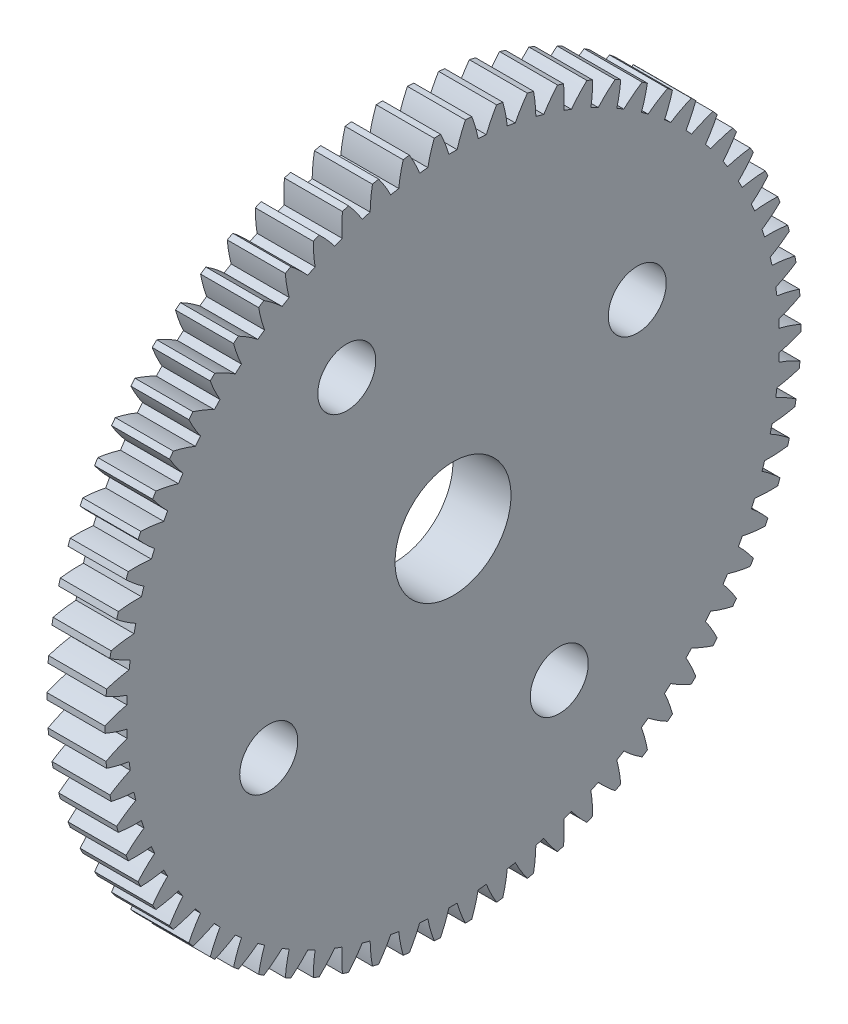
SolidWorks part; units mm, degrees
ref_plane "Plane1" through (0, 0, 0) normal (0, 0, 1) x (1, 0, 0)
ref_plane "Plane2" through (0, 0, 0) normal (0, 1, 0) x (1, 0, 0)
ref_plane "Plane3" through (0, 0, 0) normal (1, 0, 0) x (0, 0, -1)
sketch "HoldingSke" plane through (0, 0, 0) normal (0, 1, 0) x (1, 0, 0)
  line L0 (0, 0) -> (0.684, -1.8794)
  line L1 (-15, 0) -> (100, 0) construction
  line L2 (0, 0) -> (-2.1039, 2.3779)
  line L3 (0, 0) -> (-11.863, 4.5341)
  line L4 (0, 0) -> (2.9537, 8.1152)
  line L5 (0, 0) -> (-7.4956, -2.7956)
  line L6 (0, 0) -> (-2.4869, -1.6779)
  line L7 (-2.1039, 2.3779) -> (-0.3819, 10.1904)
  line L8 (-76.2, 54.61) -> (-75.2, 54.61)
  line L9 (-71.009, 38.7566) -> (-53.1078, 45.2721)
  line L10 (-76.2, 71.12) -> (104.1128, 71.12)
  line L11 (0, 0) -> (-3, 0)
  line L12 (-76.2, 101.6) -> (-76.181, 101.6)
  line L13 (24.9733, 27.94) -> (52.9518, 28.4284)
  line L14 (24.9733, 27.94) -> (24.9743, 27.94)
  line L15 (24.9733, 27.94) -> (100.4006, 29.5858)
  line L16 (-63.627, -0.5) -> (-12.827, -0.5)
  circle A0 centre (0, 0) radius 3
  circle A1 centre (0, 0) radius 7
  circle A2 centre (0, 0) radius 7
  circle A3 centre (0, 0) radius 3
  dimension "MHD" = 14
  dimension "Hub_dia" = 14
  dimension "Bore" = 6
  dimension "MBD" = 6
  dimension "Num_teeth" = 70
  dimension "Pitch" = 2
  dimension "Overall_len" = 8
  dimension "Show_teeth" = 70
  dimension "Thickness" = 3
  dimension "OAL" = 8.0001
  dimension "T_dim" = 1
  dimension "Ap" = 20
  dimension "H" = 19.05
  dimension "Pitch_radius" = 180.3128
  dimension "Width" = 3
  dimension "Backlash" = 0.019
  dimension "Addendum_fac" = 1
  dimension "Dedendum_fac" = 1.25
  dimension "Clearance_fac" = 0.25
  dimension "Dedendum_add" = 0.001
  dimension "Module" = 0.5
sketch "BasProSke" plane through (0, 0, 0) normal (0, 1, 0) x (1, 0, 0)
  line L0 (-10, 0) -> (60, 0) construction
  line L1 (0, 0) -> (0, 18)
  line L2 (0, 0) -> (3, 0)
  line L3 (3, 0) -> (3, 18)
  line L4 (3, 18) -> (0, 18)
  dimension "Thickness" = 3
  dimension "Diameter" = 36
revolve "Base-Revolve" add sketch "BasProSke" angle 360 about L0
sketch "TooCutSke" plane through (0, 0, 0) normal (1, 0, 0) x (0, 0, -1)
  line L1 (0, 0) -> (0, 107) construction
  line L2 (0, 0) -> (-0.4259, 17.4948) construction
  line L3 (0, 0) -> (-1.5699, 34.9574) construction
  line L4 (-0.4259, 17.4948) -> (-0.785, 17.4787) construction
  arc A0 (0.2122, 16.8727) -> (-0.2122, 16.8727) centre (0, 0) ccw
  arc A1 (0.6565, 18.0134) -> (-0.6565, 18.0134) centre (0, 0) ccw
  circle A2 centre (0, 0) radius 17.5 construction
  circle A3 centre (0, 0) radius 16.4446 construction
  arc A4 (-0.2122, 16.8727) -> (-0.6565, 18.0134) centre (-6.9321, 14.9121) ccw
  arc A5 (0.6565, 18.0134) -> (0.2122, 16.8727) centre (6.9321, 14.9121) ccw
  dimension "Root_dia" = 33.748
  dimension "Overcut_dia" = 36.0508
  dimension "Pitch_dia" = 35
  dimension "Base_dia" = 32.8892
  dimension "Flank_rad" = 7
  dimension "Half_ang" = 2.571
  dimension "Half_CT" = 0.3594
extrude "ToothCut" cut sketch "TooCutSke" along normal through all
fillet "Breaks" [suppressed] radius 0.01
fillet "RootFillets" [suppressed] radius 0.126
pattern_circular "TeethCuts" count 70 every 5.143 about axis through (-10, 0, 0) along (1, 0, 0) of "ToothCut", "RootFillets", "Breaks"
sketch "HubNeaOneSke" plane through (0, 0, 0) normal (-1, 0, 0) x (0, 0, 1)
  circle A0 centre (0, 0) radius 7
  dimension "Diameter" = 14
sketch "HubNeaBotSke" plane through (0, 0, 0) normal (-1, 0, 0) x (0, 0, 1)
  circle A0 centre (0, 0) radius 7
  dimension "Diameter" = 14
extrude "HubNearBoth" [suppressed] add sketch "HubNeaBotSke" along normal blind 2.5
ref_plane "FarPln" through (3, 0, 0) normal (1, 0, 0) x (0, 0, -1)
sketch "HubFarSke" plane through (3, 0, 0) normal (1, 0, 0) x (0, 0, -1)
  circle A0 centre (0, 0) radius 7
  dimension "Diameter" = 14
extrude "HubFar" [suppressed] add sketch "HubFarSke" along normal blind 2.5
sketch "BorSke" plane through (0, 0, 0) normal (1, 0, 0) x (0, 0, -1)
  circle A0 centre (0, 0) radius 3
  dimension "Diameter" = 6
extrude "Bore" cut sketch "BorSke" along normal mid plane 16.0001
sketch "KeySke" plane through (0, 0, 0) normal (1, 0, 0) x (0, 0, -1)
  line L0 (-1, 0) -> (-1, 4)
  line L1 (-1, 4) -> (1, 4)
  line L2 (1, 4) -> (1, 0)
  line L3 (0, 0) -> (0, 34) construction
  line L4 (-1, 0) -> (1, 0)
  dimension "Offset" = 4
  dimension "Width" = 2
extrude "Keyway" [suppressed] cut sketch "KeySke" along normal mid plane 16.0001
pattern_circular "Keyway2" [suppressed] count 2 every 90 about axis through (-10, 0, 0) along (1, 0, 0)
sketch "Sketch1" plane through (3, 0, 0) normal (1, 0, 0) x (0, 0, -1)
  circle A0 centre (0, 0) radius 8
  circle A1 centre (0, 8) radius 1.05
  circle A2 centre (8, 0) radius 1.05
  circle A3 centre (0, -8) radius 1.05
  circle A4 centre (-8, 0) radius 1.05
  point P14 (0, 0)
  dimension "D1" = 16
  dimension "D2" = 2.1
  dimension "D3" = 4
extrude "Cut-Extrude1" [suppressed] cut sketch "Sketch1" against normal blind 10 contours A4 | A2 | A3 | A1
sketch "Sketch3" plane through (0, 0, 0) normal (-1, 0, 0) x (0, 0, 1)
  circle A0 centre (0, 0) radius 14.5
  circle A1 centre (0, 0) radius 7.5
  dimension "D1" = 29
  dimension "D2" = 15
extrude "Cut-Extrude3" cut sketch "Sketch3" against normal blind 0.5
sketch "Sketch4" plane through (0.5, 0, 0) normal (-1, 0, 0) x (0, 0, 1)
  circle A0 centre (0, 0) radius 11 construction
  circle A1 centre (5.4948, 9.5293) radius 1.5
  circle A2 centre (9.5293, -5.4948) radius 1.5
  circle A3 centre (-5.4948, -9.5293) radius 1.5
  circle A4 centre (-9.5293, 5.4948) radius 1.5
  point P14 (0, 0)
  dimension "D1" = 22
  dimension "D2" = 3
  dimension "D3" = 4
extrude "Cut-Extrude4" cut sketch "Sketch4" against normal through all
equation "' \"Module@HoldingSke\" = 6.35"
equation "' \"Num_teeth@HoldingSke\" = 12"
equation "' \"Ap@HoldingSke\" =  20"
equation "' \"Ap@HoldingSke\" = 20"
equation "' \"Width@HoldingSke\" = 0.5 * 25.4"
equation "' \"Hub_dia@HoldingSke\"= 1 * 25.4"
equation "' \"Hub_dia@HoldingSke\" = 1 * 25.4"
equation "' \"Overall_len@HoldingSke\" = 1.0 * 25.4"
equation "' \"Bore@HoldingSke\" = 0.75 * 25.4"
equation "' \"T_dim@HoldingSke\" = 0.1 * 25.4"
equation "' \"Width@KeySke\" = 0.25 * 25.4"
equation "' \"Show_teeth@HoldingSke\" = 13"
equation "' \"Backlash@HoldingSke\" = 0.009 * 25.4"
equation "' \"Addendum_fac@HoldingSke\" = 1.0"
equation "' \"Dedendum_fac@HoldingSke\" = 1.25"
equation "' \"Dedendum_add@HoldingSke\" = 0.00005 * 25.4"
equation "' \"Clearance_fac@HoldingSke\" = 0.25"
equation "\"Pitch@HoldingSke\" = 1 / \"Module@HoldingSke\""
equation "\"Overcut_dia@TooCutSke\" = (\"Num_teeth@HoldingSke\" + 2 * \"Addendum_fac@HoldingSke\") / \"Pitch@HoldingSke\" + 0.002 * 25.4"
equation "\"Pitch_dia@TooCutSke\" = \"Num_teeth@HoldingSke\" / \"Pitch@HoldingSke\""
equation "\"Base_dia@TooCutSke\" = \"Num_teeth@HoldingSke\" / \"Pitch@HoldingSke\" * cos((\"Ap@HoldingSke\"  * 3.14159265 / 180))"
equation "\"Root_dia@TooCutSke\" = (\"Num_teeth@HoldingSke\" + 2) / \"Pitch@HoldingSke\" - 2 * (\"Addendum_fac@HoldingSke\" + \"Dedendum_fac@HoldingSke\") / \"Pitch@HoldingSke\" - \"Dedendum_add@HoldingSke\" * 2"
equation "\"Half_ang@TooCutSke\" = 180 / \"Num_teeth@HoldingSke\""
equation "\"Half_CT@TooCutSke\" = \"Num_teeth@HoldingSke\" / \"Pitch@HoldingSke\" * sin((3.14159265 / 2 / \"Num_teeth@HoldingSke\")) / 2 - 7 * \"Backlash@HoldingSke\" / 4"
equation "\"Flank_rad@TooCutSke\" = \"Num_teeth@HoldingSke\" / \"Pitch@HoldingSke\" / 5"
equation "\"Radius@RootFillets\" = \"Clearance_fac@HoldingSke\" / \"Pitch@HoldingSke\" + \"Dedendum_add@HoldingSke\""
equation "\"Break_rad@Breaks\" = 0.02 / \"Pitch@HoldingSke\""
equation "\"Thickness@HoldingSke\" = \"Width@HoldingSke\""
equation "\"OAL@HoldingSke\" = \"Thickness@HoldingSke\""
equation "\"MHD@HoldingSke\" = (\"Num_teeth@HoldingSke\" + 2) / \"Pitch@HoldingSke\" - 2 * (\"Addendum_fac@HoldingSke\" + \"Dedendum_fac@HoldingSke\")  / \"Pitch@HoldingSke\" - \"Dedendum_add@HoldingSke\" * 2"
equation "\"MBD@HoldingSke\" = (\"Num_teeth@HoldingSke\" + 2) / \"Pitch@HoldingSke\" - 2 * (\"Addendum_fac@HoldingSke\" + \"Dedendum_fac@HoldingSke\")  / \"Pitch@HoldingSke\" - \"Dedendum_add@HoldingSke\" * 2 - 0.002 * 25.4"
equation "\"MHD@HoldingSke\" = ((sgn( \"MHD@HoldingSke\" - \"Hub_dia@HoldingSke\" )-1)*( \"MHD@HoldingSke\" - \"Hub_dia@HoldingSke\" ))/-2+ \"Hub_dia@HoldingSke\""
equation "\"MBD@HoldingSke\" = ((sgn( \"MBD@HoldingSke\" - \"Bore@HoldingSke\" )-1)*( \"MBD@HoldingSke\" - \"Bore@HoldingSke\" ))/-2+ \"Bore@HoldingSke\""
equation "\"OAL@HoldingSke\" = ((sgn( \"OAL@HoldingSke\" - \"Overall_len@HoldingSke\" )+1)*( \"OAL@HoldingSke\" - \"Overall_len@HoldingSke\" ))/2 + \"Overall_len@HoldingSke\" + 0.000002 * 25.4"
equation "\"Num_teeth@TeethCuts\" = int( \"Show_teeth@HoldingSke\" ) + 1"
equation "\"Num_teeth@TeethCuts\" = ((sgn( \"Num_teeth@TeethCuts\" - \"Num_teeth@HoldingSke\" )-1)*( \"Num_teeth@TeethCuts\" - \"Num_teeth@HoldingSke\" ))/-2+ \"Num_teeth@HoldingSke\""
equation "\"Num_teeth@TeethCuts\" = ((sgn( \"Num_teeth@TeethCuts\" - 2.0)+1)*( \"Num_teeth@TeethCuts\" - 2.0))/2 +2.0"
equation "\"Angle@TeethCuts\" = 360.0 / \"Num_teeth@HoldingSke\""
equation "\"Diameter@BasProSke\" = (\"Num_teeth@HoldingSke\" + 2 * \"Addendum_fac@HoldingSke\") / \"Pitch@HoldingSke\""
equation "\"Thickness@BasProSke\"  = \"Thickness@HoldingSke\""
equation "' \"Fillet_rad@BasProSke\" =  \"Thickness@HoldingSke\" * 0.05"
equation "' \"Fillet_rad@BasProSke\" = \"Thickness@HoldingSke\" * 0.05"
equation "\"MHD@HoldingSke\" = ((sgn( \"MHD@HoldingSke\" - \"Root_dia@TooCutSke\" )-1)*( \"MHD@HoldingSke\" - \"Root_dia@TooCutSke\" ))/-2+ \"Root_dia@TooCutSke\""
equation "\"Diameter@HubNeaOneSke\" = \"MHD@HoldingSke\""
equation "\"Diameter@HubNeaBotSke\" = \"MHD@HoldingSke\""
equation "\"Length@HubNearBoth\" = ( \"OAL@HoldingSke\" - \"Thickness@BasProSke\" ) / 2.0"
equation "\"Thickness@FarPln\" = \"Thickness@BasProSke\""
equation "\"Diameter@HubFarSke\" = \"MHD@HoldingSke\""
equation "\"Length@HubFar\" = ( \"OAL@HoldingSke\" - \"Thickness@BasProSke\" ) / 2.0"
equation "\"Diameter@BorSke\" = \"MBD@HoldingSke\""
equation "\"D1@Bore\" = \"OAL@HoldingSke\" * 2.0"
equation "\"D1@Keyway\" = \"OAL@HoldingSke\" * 2.0"
equation "\"Offset@KeySke\" = \"T_dim@HoldingSke\" + \"MBD@HoldingSke\" / 2.0"
